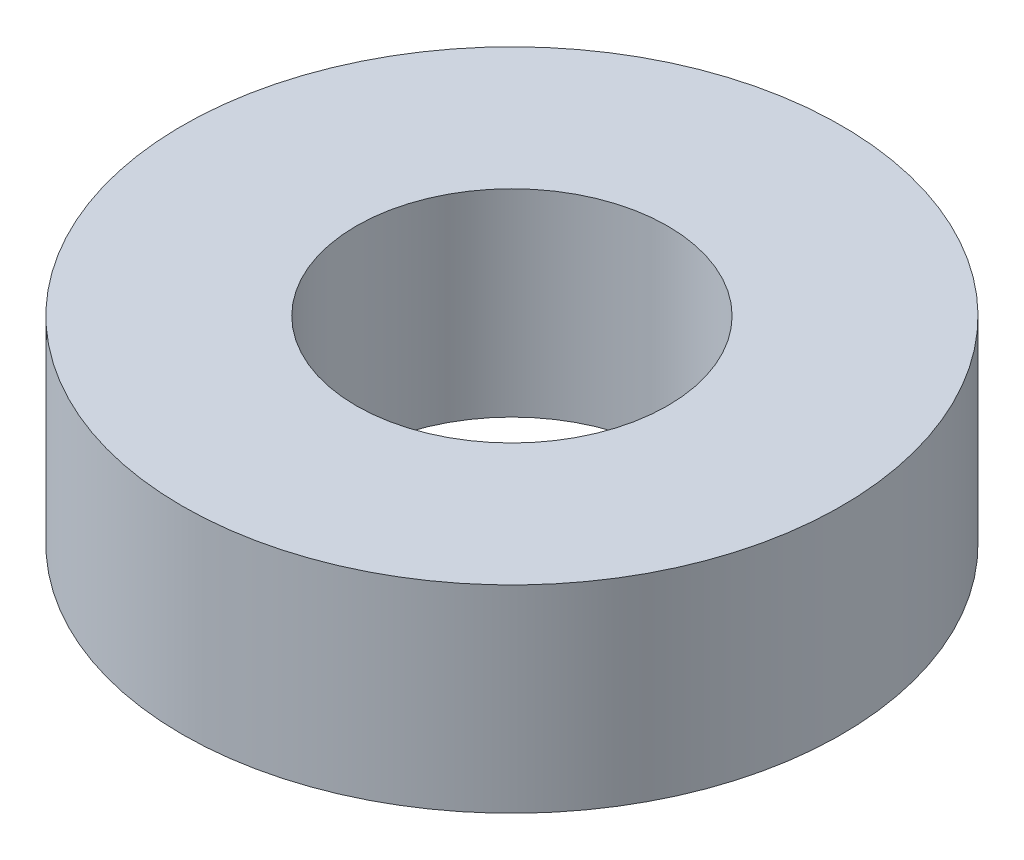
SolidWorks part; units mm, degrees
ref_plane "Front Plane" through (0, 0, 0) normal (0, 0, 1) x (1, 0, 0)
ref_plane "Top Plane" through (0, 0, 0) normal (0, 1, 0) x (1, 0, 0)
ref_plane "Right Plane" through (0, 0, 0) normal (1, 0, 0) x (0, 0, -1)
sketch "Sketch1" plane through (0, 0, 0) normal (0, 1, 0) x (1, 0, 0)
  circle A0 centre (0, 0) radius 6.35
  circle A1 centre (0, 0) radius 3
  dimension "D1" = 6
  dimension "D2" = 12.7
extrude "Boss-Extrude1" add sketch "Sketch1" along normal blind 3.81
